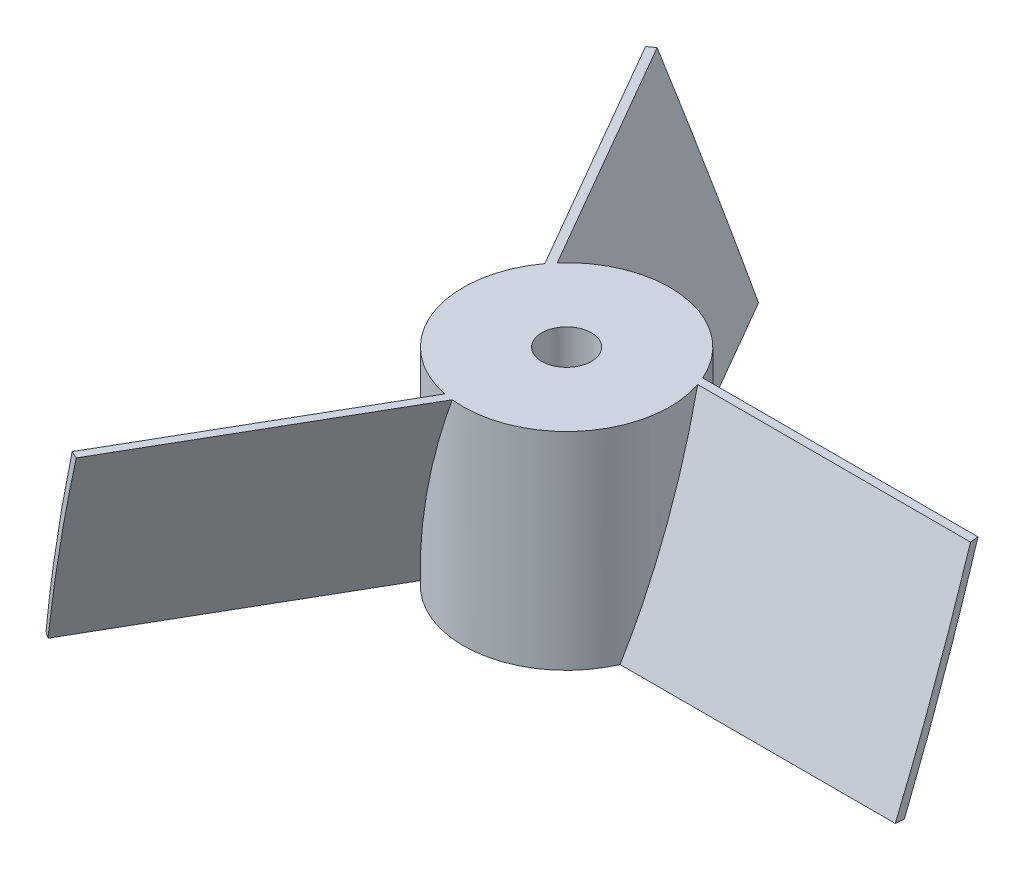
SolidWorks part; units mm, degrees
ref_plane "Front Plane" through (0, 0, 0) normal (0, 0, 1) x (1, 0, 0)
ref_plane "Top Plane" through (0, 0, 0) normal (0, 1, 0) x (1, 0, 0)
ref_plane "Right Plane" through (0, 0, 0) normal (1, 0, 0) x (0, 0, -1)
sketch "Sketch2" plane through (0, 0, 0) normal (0, 1, 0) x (1, 0, 0)
  circle A0 centre (0, 0) radius 25
  dimension "D1" = 50
extrude "Boss-Extrude1" add sketch "Sketch2" along normal blind 50
sketch "Sketch4" plane through (0, 0, 0) normal (1, 0, 0) x (0, 0, -1)
  line L0 (0, -1000) -> (0, 49000) construction
  line L1 (10, 50) -> (8, 50)
  line L2 (25, 50) -> (-25, 50) construction
  line L3 (8, 50) -> (-10, 0)
  line L4 (-25, 0) -> (25, 0) construction
  line L5 (-10, 0) -> (-8, 0)
  line L6 (-8, 0) -> (10, 50)
  line L7 (-1000, 0) -> (49000, 0) construction
  dimension "D1" = 2
  dimension "D2" = 8
  dimension "8" = 8
extrude "Boss-Extrude2" add sketch "Sketch4" along normal blind 100
pattern_circular "CirPattern1" count 3 over 360 about axis through (0, 0, 0) along (0, 1, 0) of "Boss-Extrude2"
sketch "Sketch5" plane through (0, 50, 0) normal (0, 1, 0) x (1, 0, 0)
  circle A0 centre (0, 0) radius 90
  circle A1 centre (0, 0) radius 150
  dimension "D1" = 180
  dimension "D2" = 300
extrude "Cut-Extrude3" cut sketch "Sketch5" against normal through all
sketch "Sketch3" plane through (0, 50, 0) normal (0, 1, 0) x (1, 0, 0)
  circle A0 centre (0, 0) radius 6
  dimension "D1" = 12
extrude "Cut-Extrude1" cut sketch "Sketch3" against normal through all
